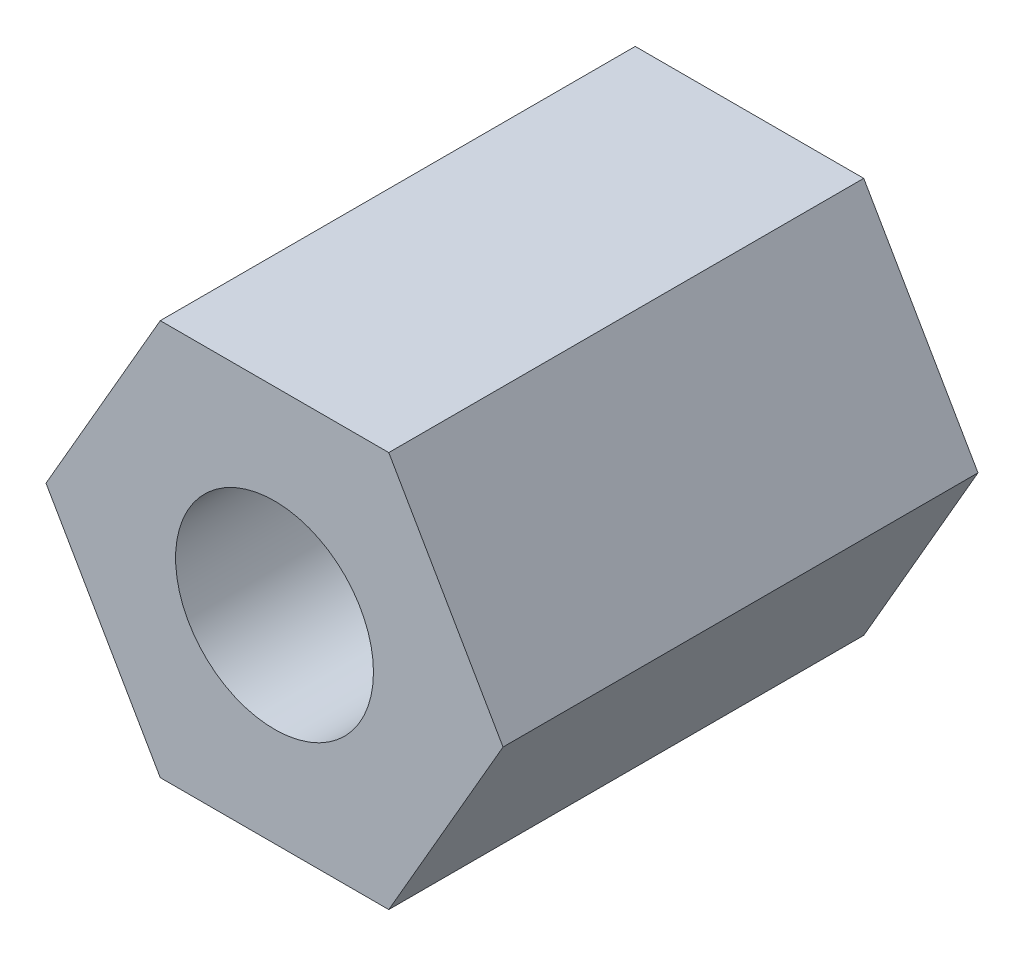
SolidWorks part; units mm, degrees
material "1.5714 (16NiCr4)"
ref_plane "Piano frontale" through (0, 0, 0) normal (0, 0, 1) x (1, 0, 0)
ref_plane "Piano superiore" through (0, 0, 0) normal (0, 1, 0) x (1, 0, 0)
ref_plane "Piano destro" through (0, 0, 0) normal (1, 0, 0) x (0, 0, -1)
sketch "Schizzo1" plane through (0, 0, 0) normal (0, 0, 1) x (1, 0, 0)
  line L1 (1.4434, 2.5) -> (-1.4434, 2.5)
  line L2 (-1.4434, 2.5) -> (-2.8868, 0)
  line L3 (-2.8868, 0) -> (-1.4434, -2.5)
  line L4 (-1.4434, -2.5) -> (1.4434, -2.5)
  line L5 (1.4434, -2.5) -> (2.8868, 0)
  line L6 (2.8868, 0) -> (1.4434, 2.5)
  circle A0 centre (0, 0) radius 2.5 construction
  dimension "D1" = 5
extrude "Estrusione-Estrusione1" add sketch "Schizzo1" along normal mid plane 6
sketch "Schizzo2" plane through (0, 0, 3) normal (0, 0, 1) x (1, 0, 0)
  circle A0 centre (0, 0) radius 1.25
  dimension "D1" = 2.5
extrude "Taglio-Estrusione1" cut sketch "Schizzo2" against normal through all
